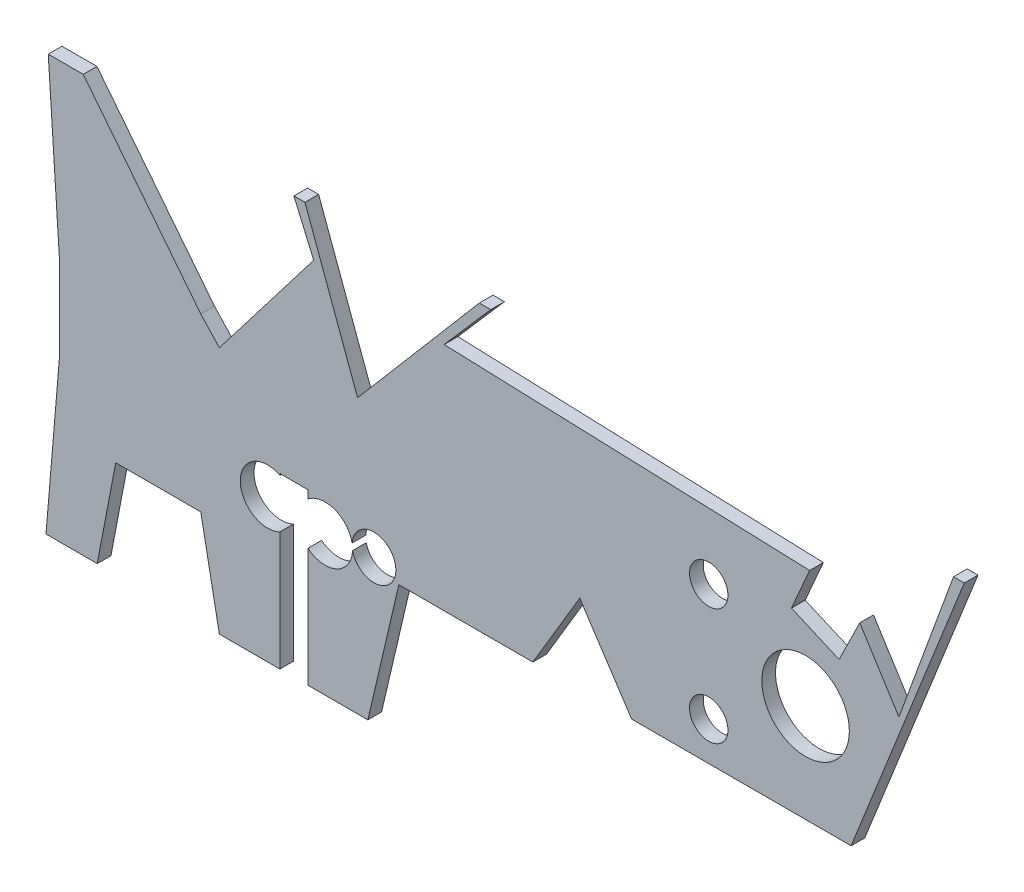
SolidWorks part; units mm, degrees
ref_plane "Спереди" through (0, 0, 0) normal (0, 0, 1) x (1, 0, 0)
ref_plane "Сверху" through (0, 0, 0) normal (0, 1, 0) x (1, 0, 0)
ref_plane "Справа" through (0, 0, 0) normal (1, 0, 0) x (0, 0, -1)
sketch "Эскиз1" plane through (0, 0, 0) normal (0, 0, 1) x (1, 0, 0)
  line L1 (-45.6294, 45.449) -> (128.4622, 45.449)
  line L2 (-45.6294, 45.449) -> (-45.6294, -15.3741)
  line L3 (-45.6294, -15.3741) -> (128.4622, -15.3741)
  line L4 (128.4622, 45.449) -> (128.4622, -15.3741)
  point P0 (0, 0)
extrude "Бобышка-Вытянуть1" add sketch "Эскиз1" along normal blind 2
sketch "Эскиз4" plane through (0, 0, 2) normal (0, 0, 1) x (1, 0, 0)
  line L0 (-1501.0978, 336.3097) -> (-192.4312, 336.3097) construction
sketch "Эскиз6" plane through (0, 0, 2) normal (0, 0, 1) x (1, 0, 0)
  line L0 (-434.7617, -109.8176) -> (2.5717, -109.8176) construction
sketch "Эскиз2" plane through (0, 0, 2) normal (0, 0, 1) x (1, 0, 0)
  circle A1 centre (-19.7853, 17.4259) radius 6.75
  circle A4 centre (26.7915, 5.539) radius 4
  circle A6 centre (35.1785, 5.0521) radius 4
  circle A7 centre (105.2973, 18.3213) radius 6.3876
extrude "Вырез-Вытянуть2" cut sketch "Эскиз2" against normal through all
sketch "Эскиз5" plane through (0, 0, 2) normal (0, 0, 1) x (1, 0, 0)
  line L0 (28.5707, 9.3476) -> (28.5707, -16.1233)
  line L2 (28.5707, -16.1233) -> (32.6663, -16.1233)
  line L3 (32.6663, -16.1233) -> (32.6663, 9.3305)
  line L4 (32.6663, 9.3305) -> (28.5707, 9.3476)
  line L6 (33.5037, 38.7656) -> (19.7382, 20.8188)
  line L8 (31.6622, 46.9835) -> (39.9102, 24.5874)
  line L9 (39.9102, 24.5874) -> (58.9886, 46.9835)
  line L10 (58.9886, 46.9835) -> (31.6622, 46.9835)
  line L11 (-4.9639, 51.5727) -> (17.0249, 23.7341)
  line L12 (17.0249, 23.7341) -> (19.7382, 20.8188)
  line L13 (4.6117, -1.2815) -> (17.0249, -1.2815)
  line L14 (17.0249, -1.2815) -> (19.7382, -15.3741)
  line L15 (-45.6294, -15.3741) -> (128.4622, -15.3741) construction
  line L16 (19.7382, -15.3741) -> (1.9155, -15.3741)
  line L17 (1.9155, -15.3741) -> (4.6117, -1.2815)
  line L18 (-5.5633, -15.3741) -> (-3.5704, 8.2808)
  line L19 (-3.5704, 8.2808) -> (-3.5704, 19.8747)
  line L20 (-3.5704, 19.8747) -> (-5.5633, 50.4752)
  line L21 (-5.5633, 50.4752) -> (-48.0137, 50.4752)
  line L22 (-48.0137, 50.4752) -> (-48.0137, -15.3741)
  line L23 (-48.0137, -15.3741) -> (-5.5633, -15.3741)
  line L25 (33.5037, 38.7656) -> (27.9708, 51.5727)
  line L26 (27.9708, 51.5727) -> (-4.9639, 51.5727)
  line L27 (72.3373, 15.4602) -> (65.4926, 3.9708)
  line L28 (65.4926, 3.9708) -> (45.9362, 3.9708)
  line L29 (45.9362, 3.9708) -> (41.4164, -15.3741)
  line L30 (41.4164, -15.3741) -> (128.4622, -15.3741)
  line L31 (128.4622, -15.3741) -> (128.4622, 45.449)
  line L32 (128.4622, 45.449) -> (111.9389, 3.9708)
  line L34 (111.9389, 3.9708) -> (79.9154, 3.9708)
  line L35 (79.9154, 3.9708) -> (72.3373, 15.4602)
  line L36 (61.0924, 47.4497) -> (52.5446, 37.636)
  line L37 (52.5446, 37.636) -> (105.8887, 35.7499)
  line L38 (105.8887, 35.7499) -> (103.2423, 29.6709)
  line L39 (103.2423, 29.6709) -> (110.1908, 26.6459)
  line L42 (113.2077, 32.7899) -> (118.9192, 23.7341)
  line L43 (118.9192, 23.7341) -> (126.8894, 45.449)
  line L45 (126.8894, 45.449) -> (61.0924, 47.4497)
  line L47 (113.2077, 32.7899) -> (110.1908, 26.6459)
  circle A0 centre (91.1621, 26.6459) radius 2.8
  circle A1 centre (91.1621, 9.6) radius 2.8
  circle A2 centre (42.2969, 5.6026) radius 3.2
  point P36 (42.2969, 5.6026)
  point P37 (0, 0)
  point P45 (91.1621, 26.6459)
  point P48 (91.1621, 10.0706)
  point P49 (91.1621, 26.6459)
  point P50 (52.5446, 37.636)
  point P51 (113.2077, 32.7899)
  point P52 (118.9192, 23.7341)
extrude "Вырез-Вытянуть6" cut sketch "Эскиз5" against normal through all
